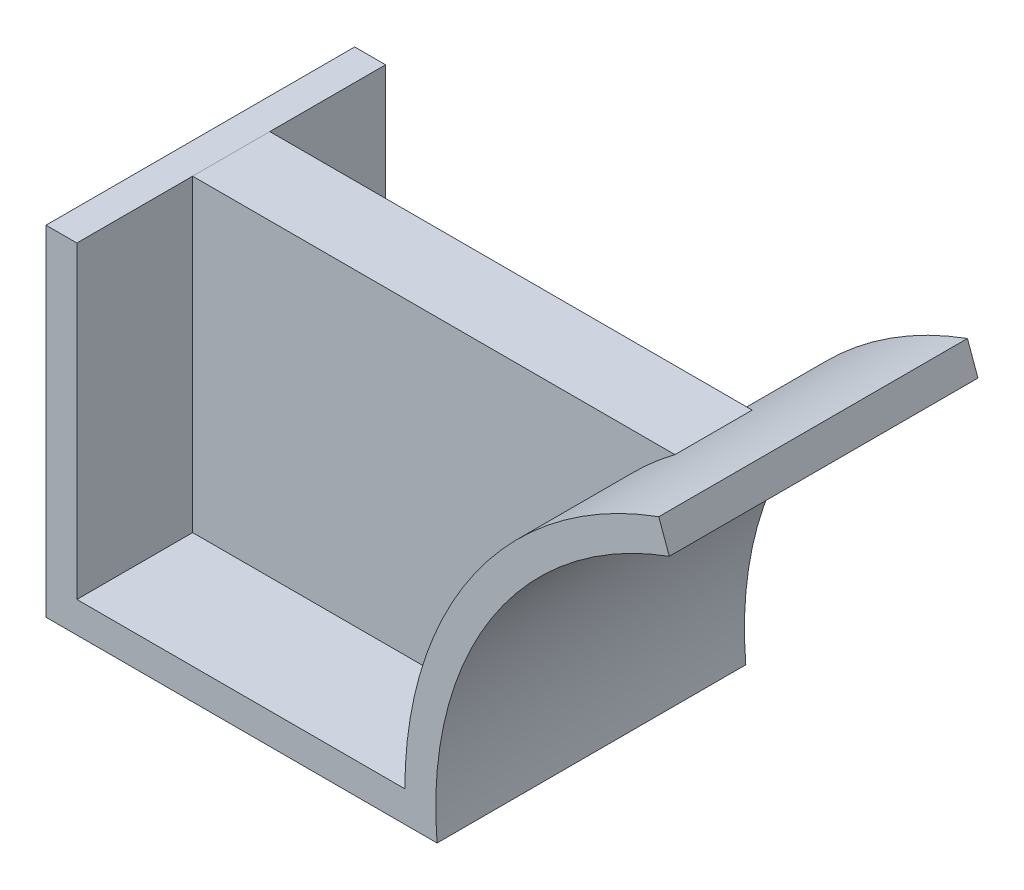
SolidWorks part; units mm, degrees
ref_plane "Front Plane" through (0, 0, 0) normal (0, 0, 1) x (1, 0, 0)
ref_plane "Top Plane" through (0, 0, 0) normal (0, 1, 0) x (1, 0, 0)
ref_plane "Right Plane" through (0, 0, 0) normal (1, 0, 0) x (0, 0, -1)
sketch "Sketch1" plane through (0, 0, 0) normal (0, 0, 1) x (1, 0, 0)
  line L0 (0, 0) -> (0, 80)
  line L1 (0, 0) -> (85, 0)
  line L2 (150.798, 93.9693) -> (185, 0) construction
  line L3 (185, 0) -> (85, 0) construction
  arc A0 (85, 0) -> (150.798, 93.9693) centre (185, 0) cw
  dimension "D3" = 100
  dimension "D1" = 80
  dimension "D2" = 85
  dimension "D4" = 70
extrude "Extrude-Thin1" add sketch "Sketch1" along normal blind 80 thin thin type one direction wall 8
sketch "Sketch2" plane through (0, 0, 0) normal (1, 0, 0) x (0, 0, -1)
  line L0 (-80, 0) -> (0, 0) construction
  line L1 (-50, 0) -> (-30, 0)
  line L2 (-50, 0) -> (-50, 80)
  line L3 (-50, 80) -> (-30, 80)
  line L4 (-30, 0) -> (-30, 80)
  line L5 (-80, 80) -> (0, 80) construction
  line L6 (-50, 0) -> (-80, 0) construction
  line L7 (-80, 86.4517) -> (-80, -8) construction
  line L8 (-30, 0) -> (0, 0) construction
  dimension "D1" = 20
extrude "Boss-Extrude2" add sketch "Sketch2" along normal up to next separate body
